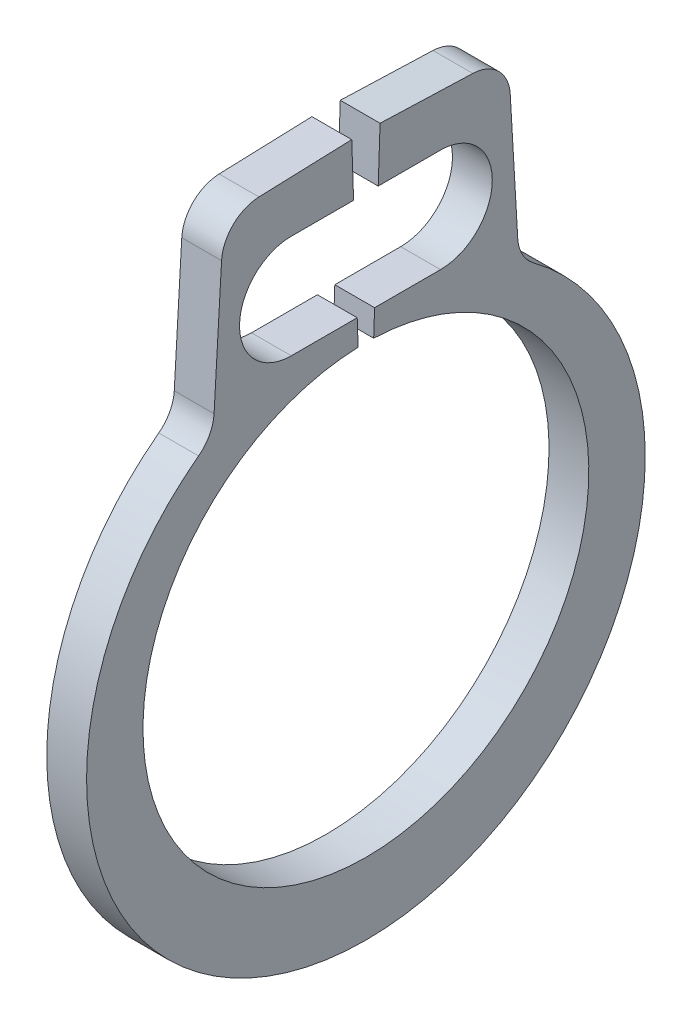
SolidWorks part; units mm, degrees
ref_plane "Front" through (0, 0, 0) normal (0, 0, 1) x (1, 0, 0)
ref_plane "Top" through (0, 0, 0) normal (0, 1, 0) x (1, 0, 0)
ref_plane "Right" through (0, 0, 0) normal (1, 0, 0) x (0, 0, -1)
sketch "Sketch1" plane through (0, 0, 0) normal (1, 0, 0) x (0, 0, -1)
  line L0 (0, 0) -> (0, 1.4224) construction
  line L1 (-0.0496, 1.4215) -> (-0.0904, 2.5892)
  line L2 (0.0904, 2.5892) -> (0.9078, 2.5607)
  line L3 (0.9078, 2.5607) -> (0.9758, 1.3943)
  line L4 (0.0496, 1.4215) -> (0.0904, 2.5892)
  line L5 (-0.0904, 2.5892) -> (-0.9078, 2.5607)
  line L6 (-0.9078, 2.5607) -> (-0.9758, 1.3943)
  line L7 (-0.9758, 1.3943) -> (-0.8156, 1.1654) construction
  line L8 (0.9758, 1.3943) -> (0.8156, 1.1654) construction
  line L9 (0, -1.4224) -> (0, -1.8796) construction
  line L10 (-0.4991, 2.5749) -> (-0.4762, 1.9177) construction
  line L11 (0, 1.4224) -> (0, 2.5908) construction
  line L12 (-1.4224, 0) -> (1.4224, 0) construction
  line L13 (0.4762, 1.5875) -> (-0.4762, 1.5875)
  line L14 (-0.4762, 2.2479) -> (0.4762, 2.2479)
  line L15 (0.4762, 1.9177) -> (-0.4762, 1.9177) construction
  circle A0 centre (0, 0) radius 1.4224 construction
  arc A1 (-0.0496, 1.4215) -> (0.0496, 1.4215) centre (0, 0) ccw
  circle A2 centre (0, 0) radius 1.5875 construction
  circle A3 centre (0, -0.0973) radius 1.4859 construction
  circle A4 centre (-0.4762, 1.9177) radius 0.3302
  circle A5 centre (0.4762, 1.9177) radius 0.3302
  arc A6 (-0.9758, 1.3943) -> (0.9758, 1.3943) centre (0, -0.0973) ccw construction
  point P0 (0, -1.8796)
  point P34 (0, 1.9177)
  point P37 (-0.4991, 2.5749)
  dimension "Ring ID" = 2.8448
  dimension "Hole Diameter" = 0.6604
  dimension "Min. Sec." = 0.2794
  dimension "Max. Sec." = 0.4572
  dimension "Lug Height" = 1.1684
  dimension "D2" = 0.8179
  dimension "Angle" = 2
sketch "Sketch2" plane through (0, 0, 0) normal (0, 0, 1) x (1, 0, 0)
  line L0 (-0.127, 2.5908) -> (0.127, 2.5908) construction
  line L2 (0, -1.5875) -> (0, 1.5875) construction
  line L3 (-0.1524, -1.8796) -> (0.1524, -1.8796) construction
  point P8 (0, 2.5908)
  point P14 (0, -1.8796)
  dimension "Ring Thickness" = 0.254
  dimension "For Groove Width" = 0.3048
sketch "Sketch3" plane through (0, 0, 0) normal (1, 0, 0) x (0, 0, -1)
  line L0 (-0.9078, 2.5607) -> (-0.9758, 1.3943) construction
  line L1 (-0.9078, 2.5607) -> (-0.9758, 1.3943)
  line L2 (-0.0904, 2.5892) -> (-0.9078, 2.5607) construction
  line L3 (-0.0904, 2.5892) -> (-0.9078, 2.5607)
  line L4 (-0.0496, 1.4215) -> (-0.0904, 2.5892) construction
  line L5 (-0.0496, 1.4215) -> (-0.0554, 1.5875)
  line L6 (0.0496, 1.4215) -> (0.0904, 2.5892) construction
  line L7 (0.0496, 1.4215) -> (0.0554, 1.5875)
  line L8 (0.0904, 2.5892) -> (0.9078, 2.5607) construction
  line L9 (0.0904, 2.5892) -> (0.9078, 2.5607)
  line L10 (0.9078, 2.5607) -> (0.9758, 1.3943) construction
  line L11 (0.9078, 2.5607) -> (0.9758, 1.3943)
  line L12 (0.4762, 1.5875) -> (-0.4762, 1.5875) construction
  line L13 (0.4762, 1.5875) -> (0.0554, 1.5875)
  line L14 (-0.4762, 2.2479) -> (0.4762, 2.2479) construction
  line L15 (-0.4762, 2.2479) -> (-0.0785, 2.2479)
  line L16 (-0.0554, 1.5875) -> (-0.4762, 1.5875)
  line L17 (0.0785, 2.2479) -> (0.4762, 2.2479)
  line L18 (-0.0785, 2.2479) -> (-0.0904, 2.5892)
  line L19 (0.0785, 2.2479) -> (0.0904, 2.5892)
  arc A0 (-0.9758, 1.3943) -> (0.9758, 1.3943) centre (0, -0.0973) ccw construction
  arc A1 (-0.9758, 1.3943) -> (0.9758, 1.3943) centre (0, -0.0973) ccw
  arc A2 (-0.0496, 1.4215) -> (0.0496, 1.4215) centre (0, 0) ccw construction
  arc A3 (-0.0496, 1.4215) -> (0.0496, 1.4215) centre (0, 0) ccw
  circle A4 centre (-0.4762, 1.9177) radius 0.3302 construction
  arc A5 (-0.4762, 2.2479) -> (-0.4762, 1.5875) centre (-0.4762, 1.9177) ccw
  circle A6 centre (0.4762, 1.9177) radius 0.3302 construction
  arc A7 (0.4762, 1.5875) -> (0.4762, 2.2479) centre (0.4762, 1.9177) ccw
extrude "Boss-Extrude1" add sketch "Sketch3" along normal up to vertex (0.127 mm away) and the other way up to vertex (0.127 mm away) up to point (0.127, 2.5908, 0) other way up to point (-0.127, 2.5908, 0)
fillet "Fillet1" radius 0.2476 4 edges at (0, 1.3943, -0.9758) (0, 2.5607, -0.9078) (0, 2.5607, 0.9078) (0, 1.3943, 0.9758)
sketch "Sketch4" plane through (0, 0, 0) normal (1, 0, 0) x (0, 0, -1)
  line L0 (-1.2318, 0.7112) -> (0, 0) construction
  line L1 (0, 0) -> (0, 1.4224) construction
  line L2 (0, 2.5908) -> (0, 1.4224) construction
  arc A0 (-0.0496, 1.4215) -> (0.0496, 1.4215) centre (0, 0) ccw construction
  point P0 (0, 0)
  point P1 (-1.2318, 0.7112)
  dimension "D1" = 60
equation "\"D2@Sketch1\"=\"Lug Height@Sketch1\" * .7"
equation "\"D1@Fillet1\"=\"Hole Diameter@Sketch1\"*.375"
